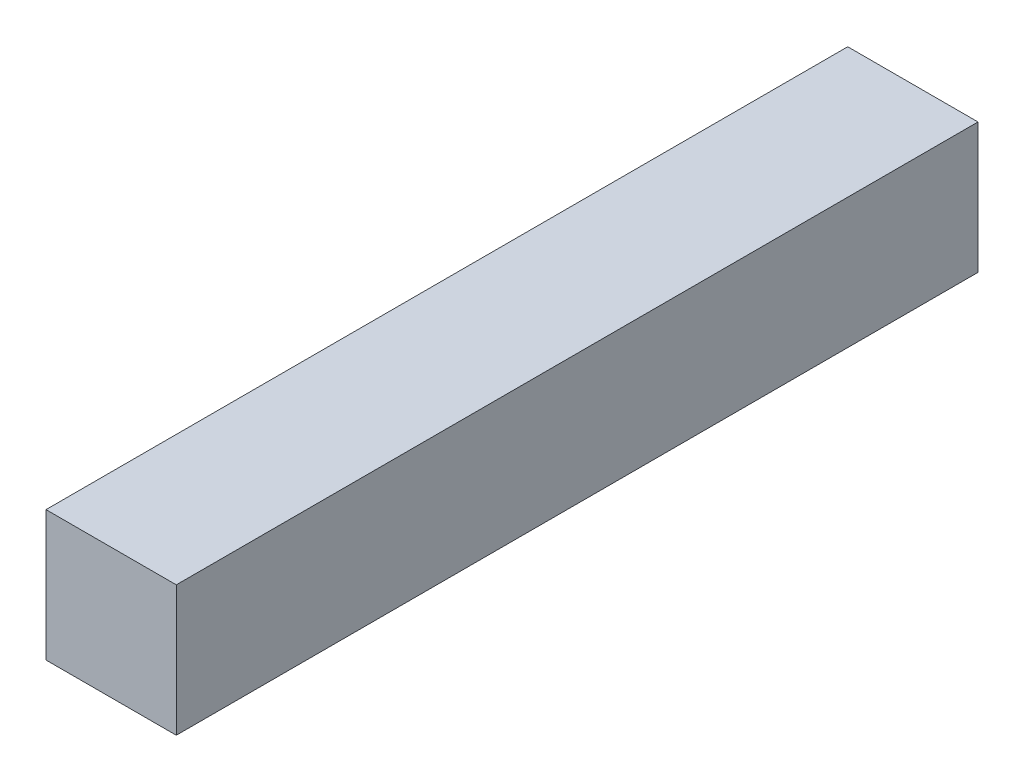
SolidWorks part; units mm, degrees
ref_plane "Front Plane" through (0, 0, 0) normal (0, 0, 1) x (1, 0, 0)
ref_plane "Top Plane" through (0, 0, 0) normal (0, 1, 0) x (1, 0, 0)
ref_plane "Right Plane" through (0, 0, 0) normal (1, 0, 0) x (0, 0, -1)
sketch "Sketch1" plane through (0, 0, 0) normal (0, 0, 1) x (1, 0, 0)
  line L1 (0, 0) -> (65, 0)
  line L2 (0, 0) -> (0, 65)
  line L3 (0, 65) -> (65, 65)
  line L4 (65, 0) -> (65, 65)
extrude "Boss-Extrude1" add sketch "Sketch1" along normal blind 400
